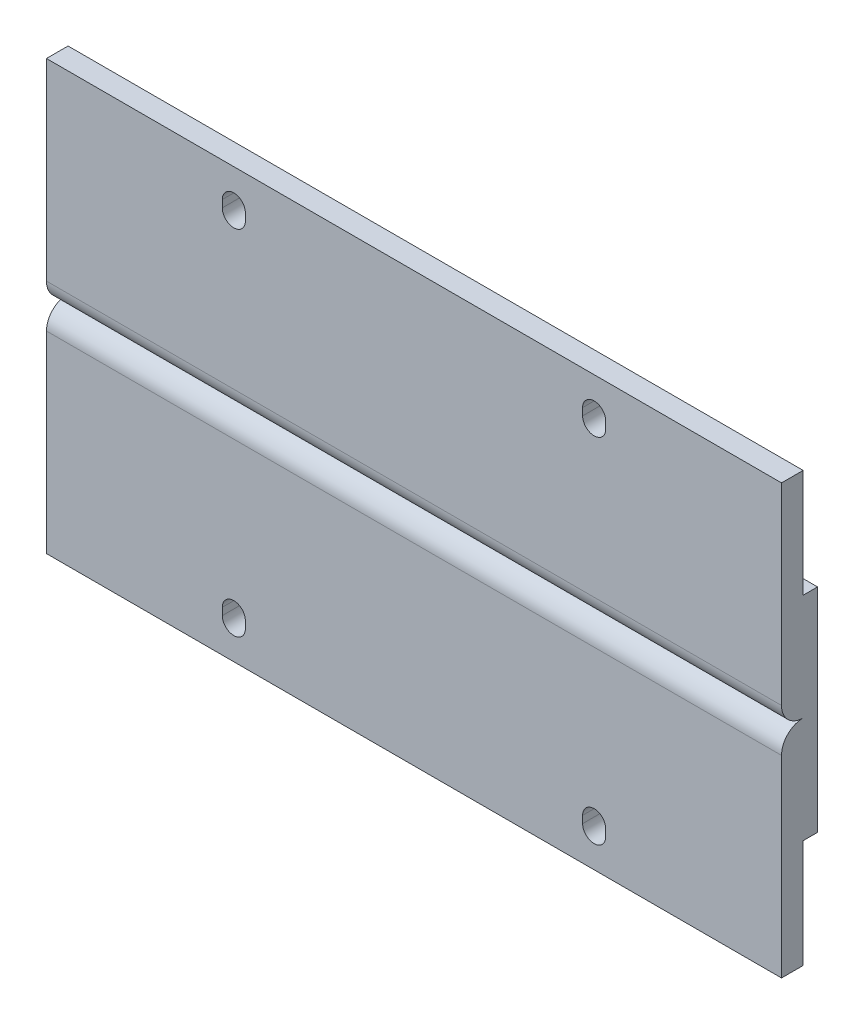
SolidWorks part; units mm, degrees
ref_plane "Front Plane" through (0, 0, 0) normal (0, 0, 1) x (1, 0, 0)
ref_plane "Top Plane" through (0, 0, 0) normal (0, 1, 0) x (1, 0, 0)
ref_plane "Right Plane" through (0, 0, 0) normal (1, 0, 0) x (0, 0, -1)
sketch "Sketch1" plane through (0, 0, 0) normal (1, 0, 0) x (0, 0, -1)
  line L0 (0, 29.75) -> (0, -29.75)
  line L1 (0, -29.75) -> (3, -29.75)
  line L2 (3, -29.75) -> (3, -14.75)
  line L3 (3, -14.75) -> (5, -14.75)
  line L4 (5, -14.75) -> (5, 14.75)
  line L5 (5, 14.75) -> (3, 14.75)
  line L6 (3, 14.75) -> (3, 29.75)
  line L7 (3, 29.75) -> (0, 29.75)
  point P2 (0, 0)
  dimension "D1" = 3
  dimension "D2" = 2
  dimension "D3" = 29.5
  dimension "D4" = 59.5
extrude "Boss-Extrude1" add sketch "Sketch1" along normal mid plane 102
sketch "Sketch3" plane through (0, 0, 0) normal (0, 0, 1) x (1, 0, 0)
  line L0 (25, 24) -> (25, 25) construction
  line L1 (-25, -24) -> (25, -24) construction
  line L2 (-25, -24) -> (-25, 24) construction
  line L3 (-25, 24) -> (25, 24) construction
  line L4 (25, -24) -> (25, 24) construction
  line L5 (-25, -24) -> (25, 24) construction
  line L6 (-25, 24) -> (25, -24) construction
  line L7 (23.4, 24) -> (23.4, 25)
  line L8 (26.6, 24) -> (26.6, 25)
  line L9 (-25, 24) -> (-25, 25) construction
  line L10 (-26.6, 24) -> (-26.6, 25)
  line L11 (-23.4, 24) -> (-23.4, 25)
  line L12 (25, -24) -> (25, -25) construction
  line L13 (26.6, -24) -> (26.6, -25)
  line L14 (23.4, -24) -> (23.4, -25)
  line L15 (-25, -24) -> (-25, -25) construction
  line L16 (-23.4, -24) -> (-23.4, -25)
  line L17 (-26.6, -24) -> (-26.6, -25)
  arc A0 (23.4, 24) -> (26.6, 24) centre (25, 24) ccw
  arc A1 (26.6, 25) -> (23.4, 25) centre (25, 25) ccw
  arc A2 (-26.6, 24) -> (-23.4, 24) centre (-25, 24) ccw
  arc A3 (-23.4, 25) -> (-26.6, 25) centre (-25, 25) ccw
  arc A4 (26.6, -24) -> (23.4, -24) centre (25, -24) ccw
  arc A5 (23.4, -25) -> (26.6, -25) centre (25, -25) ccw
  arc A6 (-23.4, -24) -> (-26.6, -24) centre (-25, -24) ccw
  arc A7 (-26.6, -25) -> (-23.4, -25) centre (-25, -25) ccw
  point P0 (0, 0)
  point P6 (25, 24.5)
  point P12 (-25, 24.5)
  point P18 (25, -24.5)
  point P24 (-25, -24.5)
  dimension "D4" = 1.6
  dimension "D1" = 48
  dimension "D2" = 50
  dimension "D3" = 1
extrude "Cut-Extrude1" cut sketch "Sketch3" against normal through all
sketch "Sketch5" plane through (0, 0, 0) normal (0, 0, 1) x (1, 0, 0)
  line L0 (51, -29.75) -> (-51, -29.75) construction
  line L1 (-51, 29.75) -> (-38, 29.75)
  line L2 (-51, 29.75) -> (-51, -29.75)
  line L3 (-51, -29.75) -> (-38, -29.75)
  line L4 (-38, 29.75) -> (-38, -29.75)
  line L5 (51, 29.75) -> (51, -29.75) construction
  dimension "D1" = 89
extrude "Trim" [suppressed] cut sketch "Sketch5" against normal through all
sketch "Sketch6" plane through (0, 0, 0) normal (1, 0, 0) x (0, 0, -1)
  line L0 (3, 14.75) -> (3, 29.75)
  line L1 (5, 14.75) -> (3, 14.75)
  line L2 (5, -14.75) -> (5, 14.75)
  line L3 (3, -14.75) -> (5, -14.75)
  line L4 (3, -29.75) -> (3, -14.75)
  line L5 (0, -29.75) -> (3, -29.75)
  line L6 (0, 29.75) -> (0, -29.75)
  line L7 (3, 29.75) -> (0, 29.75)
  line L8 (3, 29.75) -> (0, 29.75)
  line L9 (0, 29.75) -> (0, -29.75)
  line L10 (0, -29.75) -> (3, -29.75)
  line L11 (3, -29.75) -> (3, -14.75)
  line L12 (3, -14.75) -> (5, -14.75)
  line L13 (5, -14.75) -> (5, 14.75)
  line L14 (5, 14.75) -> (3, 14.75)
  line L15 (3, 14.75) -> (3, 29.75)
  line L16 (0, 3) -> (0, -3)
  arc A0 (0, 3) -> (3, 0) centre (3, 3) ccw
  arc A1 (0, -3) -> (3, 0) centre (3, -3) cw
  dimension "D1" = 3
extrude "Greeble1" cut sketch "Sketch6" against normal through all both and the other way through all contours L9 A1 A0
equation "\"D3@Sketch1\"=30-0.5"
equation "\"D4@Sketch1\"=60-0.5"
